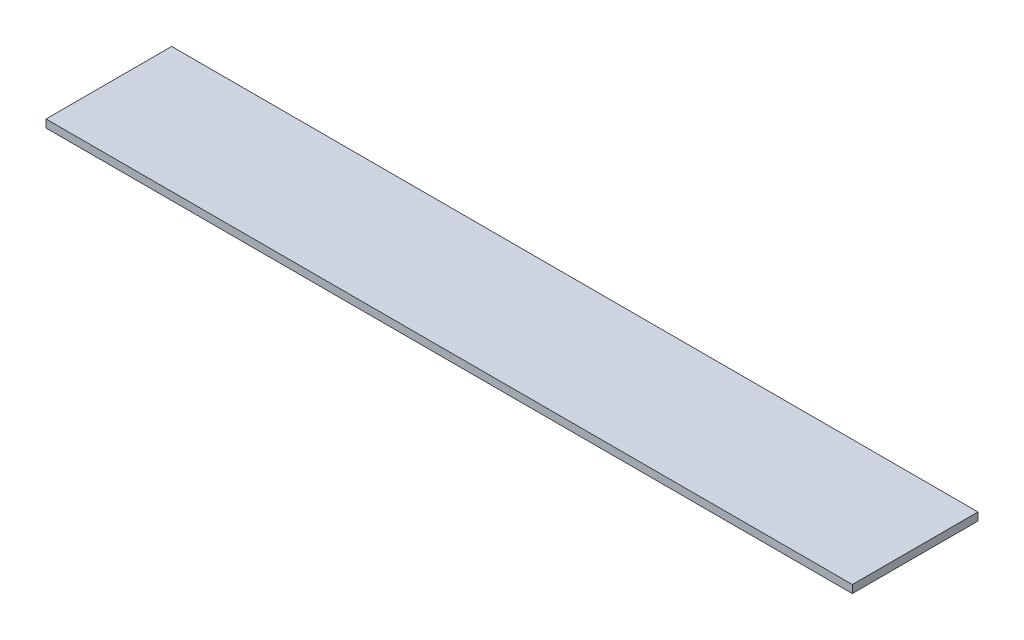
SolidWorks part; units mm, degrees
material "Balsa"
ref_plane "Alzado" through (0, 0, 0) normal (0, 0, 1) x (1, 0, 0)
ref_plane "Planta" through (0, 0, 0) normal (0, 1, 0) x (1, 0, 0)
ref_plane "Vista lateral" through (0, 0, 0) normal (1, 0, 0) x (0, 0, -1)
sketch "Croquis1" plane through (0, 0, 0) normal (0, 1, 0) x (1, 0, 0)
  line L1 (0, 0) -> (308, 0)
  line L2 (0, 0) -> (0, 48)
  line L3 (0, 48) -> (308, 48)
  line L4 (308, 0) -> (308, 48)
extrude "Saliente-Extruir1" add sketch "Croquis1" along normal blind 3
